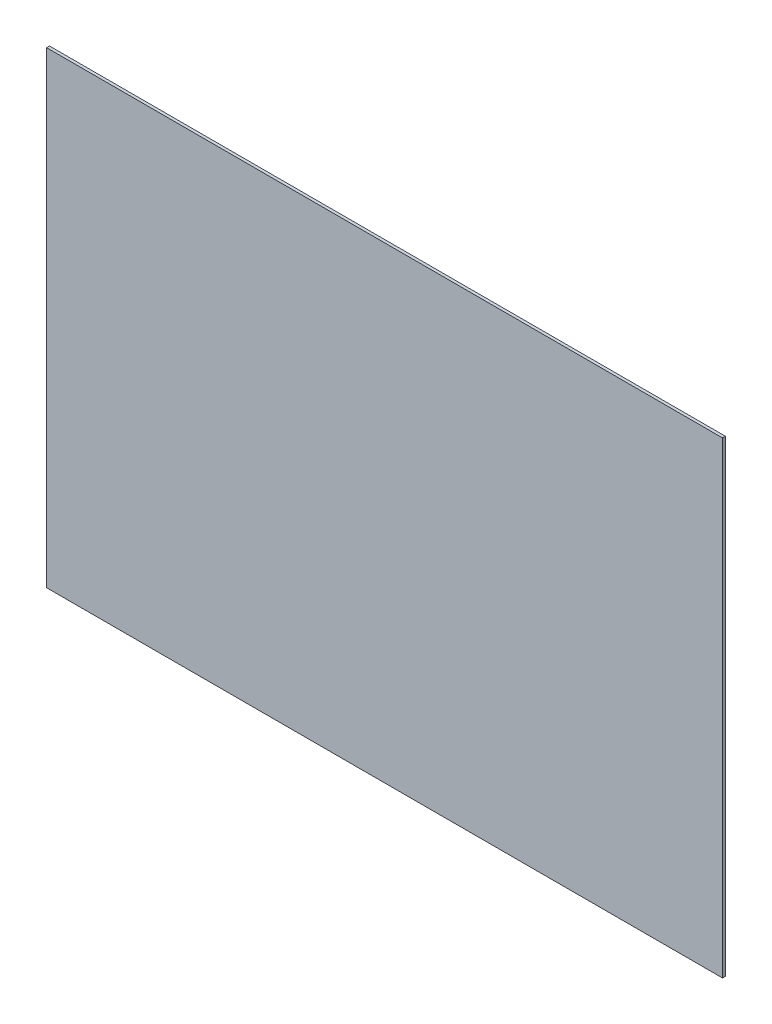
SolidWorks part; units mm, degrees
material "Mahogany"
ref_plane "Front Plane" through (0, 0, 0) normal (0, 0, 1) x (1, 0, 0)
ref_plane "Top Plane" through (0, 0, 0) normal (0, 1, 0) x (1, 0, 0)
ref_plane "Right Plane" through (0, 0, 0) normal (1, 0, 0) x (0, 0, -1)
sketch "Sketch1" plane through (0, 0, 0) normal (0, 0, 1) x (1, 0, 0)
  line L1 (-372.5, 257.8) -> (372.5, 257.8)
  line L2 (-372.5, 257.8) -> (-372.5, -257.8)
  line L3 (-372.5, -257.8) -> (372.5, -257.8)
  line L4 (372.5, 257.8) -> (372.5, -257.8)
  line L5 (-372.5, 257.8) -> (372.5, -257.8) construction
  line L6 (-372.5, -257.8) -> (372.5, 257.8) construction
  point P0 (0, 0)
  dimension "D1" = 745
  dimension "D2" = 515.6
extrude "Boss-Extrude1" add sketch "Sketch1" along normal blind 3.175
equation "\"W\"= 1700"
equation "\"L\"= 760"
equation "\"H\"= 810"
equation "\"ARM_BOLT_SPACING\"= 166"
equation "\"ARM_TO_WALL\"= 300"
equation "\"D1@Sketch1\"=\"L\"-15"
equation "\"D2@Sketch1\"=\"H\"-(15+279.4)"
